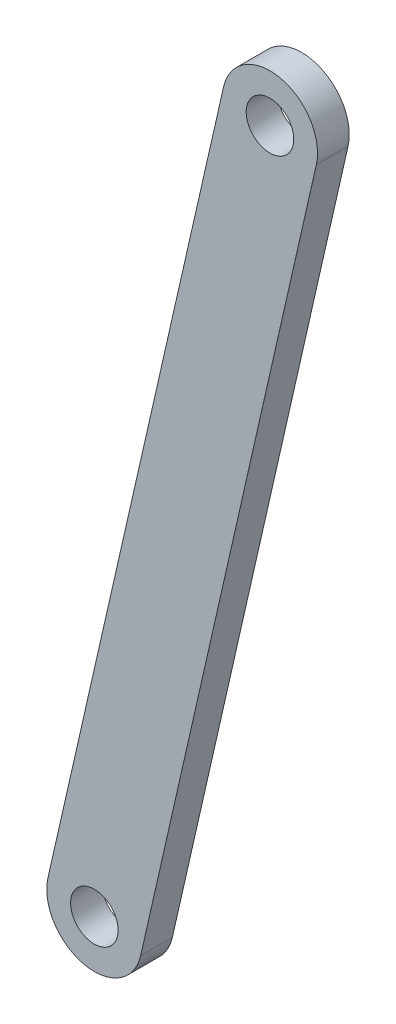
SolidWorks part; units mm, degrees
ref_plane "Front Plane" through (0, 0, 0) normal (0, 0, 1) x (1, 0, 0)
ref_plane "Top Plane" through (0, 0, 0) normal (0, 1, 0) x (1, 0, 0)
ref_plane "Right Plane" through (0, 0, 0) normal (1, 0, 0) x (0, 0, -1)
sketch "Sketch2" plane through (0, 0, 0) normal (0, 0, 1) x (1, 0, 0)
  line L0 (0, 0) -> (55.4053, 243.7832) construction
  line L1 (-14.627, 3.3243) -> (40.7783, 247.1075)
  line L2 (14.627, -3.3243) -> (70.0323, 240.4589)
  arc A0 (-14.627, 3.3243) -> (14.627, -3.3243) centre (0, 0) ccw
  arc A1 (70.0323, 240.4589) -> (40.7783, 247.1075) centre (55.4053, 243.7832) ccw
  circle A2 centre (0, 0) radius 7.5
  circle A3 centre (55.4053, 243.7832) radius 7.5
  point P3 (27.7026, 121.8916)
  dimension "D3" = 15
  dimension "D4" = 15
  dimension "D1" = 250
  dimension "D2" = 30
extrude "Boss-Extrude1" add sketch "Sketch2" along normal blind 10
